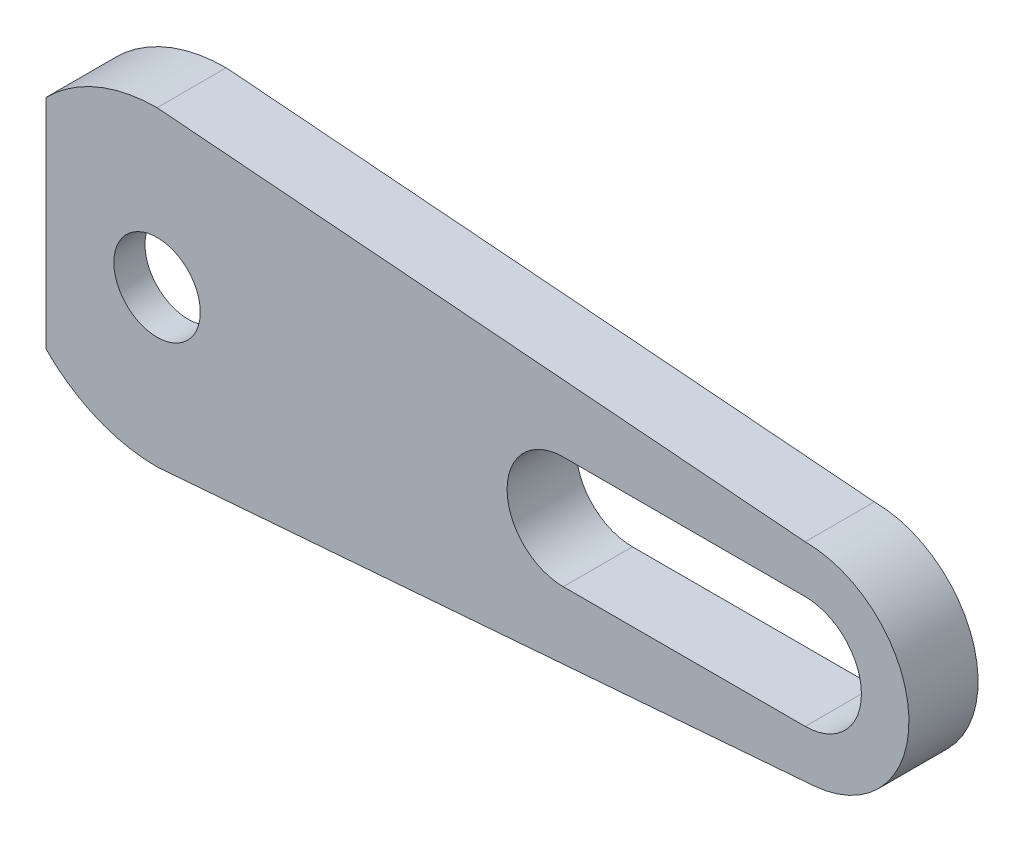
SolidWorks part; units mm, degrees
ref_plane "Front Plane" through (0, 0, 0) normal (0, 0, 1) x (1, 0, 0)
ref_plane "Top Plane" through (0, 0, 0) normal (0, 1, 0) x (1, 0, 0)
ref_plane "Right Plane" through (0, 0, 0) normal (1, 0, 0) x (0, 0, -1)
sketch "Esquisse1" plane through (0, 0, 0) normal (0, 0, 1) x (1, 0, 0)
  line L0 (-4.3758, 4.25) -> (-6.4265, 6.3008)
  line L1 (4.3758, 4.25) -> (17.3156, 2.7822)
  line L2 (17.3156, -2.7822) -> (4.3758, -4.25)
  line L3 (23.5, 3.25) -> (37.5, 3.25)
  line L4 (0, 9) -> (37.5, 6)
  line L5 (0, -9) -> (37.9755, -5.9811)
  line L6 (-4.3758, -4.25) -> (-6.4265, -6.3008)
  line L7 (23.5, -3.25) -> (37.5, -3.25)
  arc A0 (4.3758, 4.25) -> (-4.3758, 4.25) centre (0, 0) ccw
  arc A1 (17.3156, -2.7822) -> (17.3156, 2.7822) centre (17, 0) ccw
  arc A2 (4.3758, -4.25) -> (-4.3758, -4.25) centre (0, 0) cw
  arc A3 (-6.4265, 6.3008) -> (0, 9) centre (0, 0) cw
  arc A4 (37.5, 3.25) -> (37.5, -3.25) centre (37.5, 0) cw
  arc A5 (-6.4265, -6.3008) -> (0, -9) centre (0, 0) ccw
  arc A6 (37.5, 6) -> (37.9755, -5.9811) centre (37.5, 0) cw
  arc A7 (23.5, 3.25) -> (23.5, -3.25) centre (23.5, 0) ccw
  dimension "D2" = 6.1
  dimension "D3" = 2.8
  dimension "D5" = 3.25
  dimension "D6" = 9
  dimension "D8" = 37.5
  dimension "D1" = 8.5
  dimension "D4" = 17
  dimension "D7" = 23.5
  dimension "D9" = 6
  dimension "D10" = 14
extrude "Main" add sketch "Esquisse1" along normal blind 4
sketch "Esquisse2" plane through (0, 0, 4) normal (0, 0, -1) x (-1, 0, 0)
  line L0 (0, -9) -> (-12.8903, -7.9753)
  line L1 (0, -9) -> (-37.9755, -5.9811) construction
  line L2 (0, -9) -> (-37.9755, -5.9811) construction
  line L3 (0, 9) -> (-12.8903, 7.9688)
  line L4 (6.4265, -6.3008) -> (6.4265, 6.3008)
  line L5 (-37.5, 6) -> (0, 9) construction
  line L6 (-37.5, 6) -> (0, 9) construction
  line L7 (0, -9) -> (-37.9755, -5.9811) construction
  line L10 (6.4265, 6.3008) -> (4.3758, 4.25) construction
  arc A0 (6.4265, 6.3008) -> (0, 9) centre (0, 0) ccw construction
  arc A1 (0, -9) -> (6.4265, -6.3008) centre (0, 0) ccw
  circle A2 centre (0, 0) radius 2.5
  arc A3 (6.4265, 6.3008) -> (0, 9) centre (0, 0) ccw
  arc A4 (-12.8903, -7.9753) -> (-12.8903, 7.9688) centre (-12.2525, -0.0033) cw
  arc A5 (-23.5, -3.25) -> (-23.5, 3.25) centre (-23.5, 0) ccw construction
  arc A6 (0, -9) -> (6.4265, -6.3008) centre (0, 0) ccw construction
  dimension "D1" = 5
extrude "Boss-Extrude1" add sketch "Esquisse2" along normal blind 1.8
